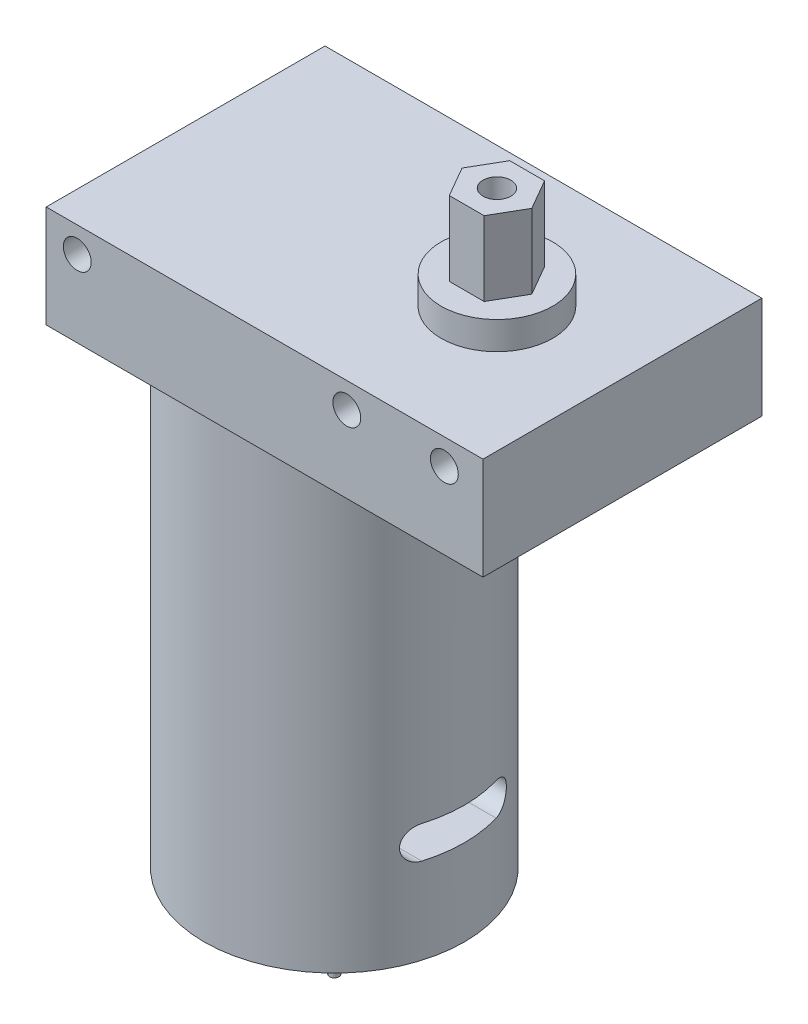
SolidWorks part; units mm, degrees
material "商用纯 CP-Ti UNS R50400 (SS)"
ref_plane "前视基准面" through (0, 0, 0) normal (0, 0, 1) x (1, 0, 0)
ref_plane "上视基准面" through (0, 0, 0) normal (0, 1, 0) x (1, 0, 0)
ref_plane "右视基准面" through (0, 0, 0) normal (1, 0, 0) x (0, 0, -1)
sketch "草图1" plane through (0, 0, 0) normal (0, 1, 0) x (1, 0, 0)
  line L1 (0, 0) -> (47, 0)
  line L2 (0, 0) -> (0, -30)
  line L3 (0, -30) -> (47, -30)
  line L4 (47, 0) -> (47, -30)
  dimension "D1" = 47
  dimension "D2" = 30
extrude "凸台-拉伸1" add sketch "草图1" along normal blind 11
sketch "草图2" plane through (0, 11, 0) normal (0, 1, 0) x (1, 0, 0)
  line L0 (47, 0) -> (0, 0) construction
  line L1 (47, -30) -> (47, 0) construction
  circle A0 centre (33.5, -15) radius 6
  dimension "D1" = 15
  dimension "D3" = 12
  dimension "D2" = 13.5
extrude "凸台-拉伸2" add sketch "草图2" along normal blind 3
sketch "草图3" plane through (0, 14, 0) normal (0, 1, 0) x (1, 0, 0)
  line L1 (37.2528, -15) -> (35.3764, -11.75)
  line L2 (35.3764, -11.75) -> (31.6236, -11.75)
  line L3 (31.6236, -11.75) -> (29.7472, -15)
  line L4 (29.7472, -15) -> (31.6236, -18.25)
  line L5 (31.6236, -18.25) -> (35.3764, -18.25)
  line L6 (35.3764, -18.25) -> (37.2528, -15)
  circle A0 centre (33.5, -15) radius 3.25 construction
  dimension "D1" = 6.5
extrude "凸台-拉伸3" add sketch "草图3" along normal blind 8
sketch "草图4" plane through (0, 0, 0) normal (0, -1, 0) x (1, 0, 0)
  line L0 (0, 30) -> (47, 30) construction
  line L1 (0, 0) -> (0, 30) construction
  circle A0 centre (16, 15) radius 14
  dimension "D1" = 15
  dimension "D3" = 28
  dimension "D2" = 16
extrude "凸台-拉伸4" add sketch "草图4" along normal blind 50
sketch "草图5" plane through (0, -50, 0) normal (0, -1, 0) x (1, 0, 0)
  circle A0 centre (16, 15) radius 5
  dimension "D1" = 10
extrude "凸台-拉伸5" add sketch "草图5" along normal blind 2
sketch "草图6" plane through (0, 0, 30) normal (0, 0, 1) x (1, 0, 0)
  line L0 (0, 11) -> (47, 11) construction
  circle A0 centre (3.3408, 8.25) radius 1.5
  circle A1 centre (32.3408, 8.25) radius 1.5
  circle A2 centre (42.8408, 8.25) radius 1.5
  dimension "D1" = 3
  dimension "D2" = 39.5
  dimension "D3" = 10.5
  dimension "D4" = 2.75
extrude "切除-拉伸1" cut sketch "草图6" against normal through all
sketch "草图7" plane through (0, 0, 0) normal (-1, 0, 0) x (0, 0, 1)
  line L0 (15, 11) -> (15, -39) construction
  line L1 (0, 11) -> (30, 11) construction
  line L2 (-10.279, -39) -> (39.7397, -39) construction
  line L3 (11, -39) -> (19, -39) construction
  line L4 (11, -37.25) -> (19, -37.25)
  line L5 (11, -40.75) -> (19, -40.75)
  arc A0 (11, -37.25) -> (11, -40.75) centre (11, -39) ccw
  arc A1 (19, -40.75) -> (19, -37.25) centre (19, -39) ccw
  point P8 (15, -39)
  dimension "D1" = 3.5
  dimension "D2" = 8
extrude "切除-拉伸2" cut sketch "草图7" against normal through all
sketch "草图9" plane through (0, 22, 0) normal (0, 1, 0) x (1, 0, 0)
  circle A0 centre (33.5, -15) radius 1.5
extrude "切除-拉伸3" cut sketch "草图9" against normal blind 8
sketch "草图11" plane through (0, -52, 0) normal (0, -1, 0) x (1, 0, 0)
  circle A0 centre (16, 15) radius 0.5
extrude "凸台-拉伸6" add sketch "草图11" along normal blind 8
